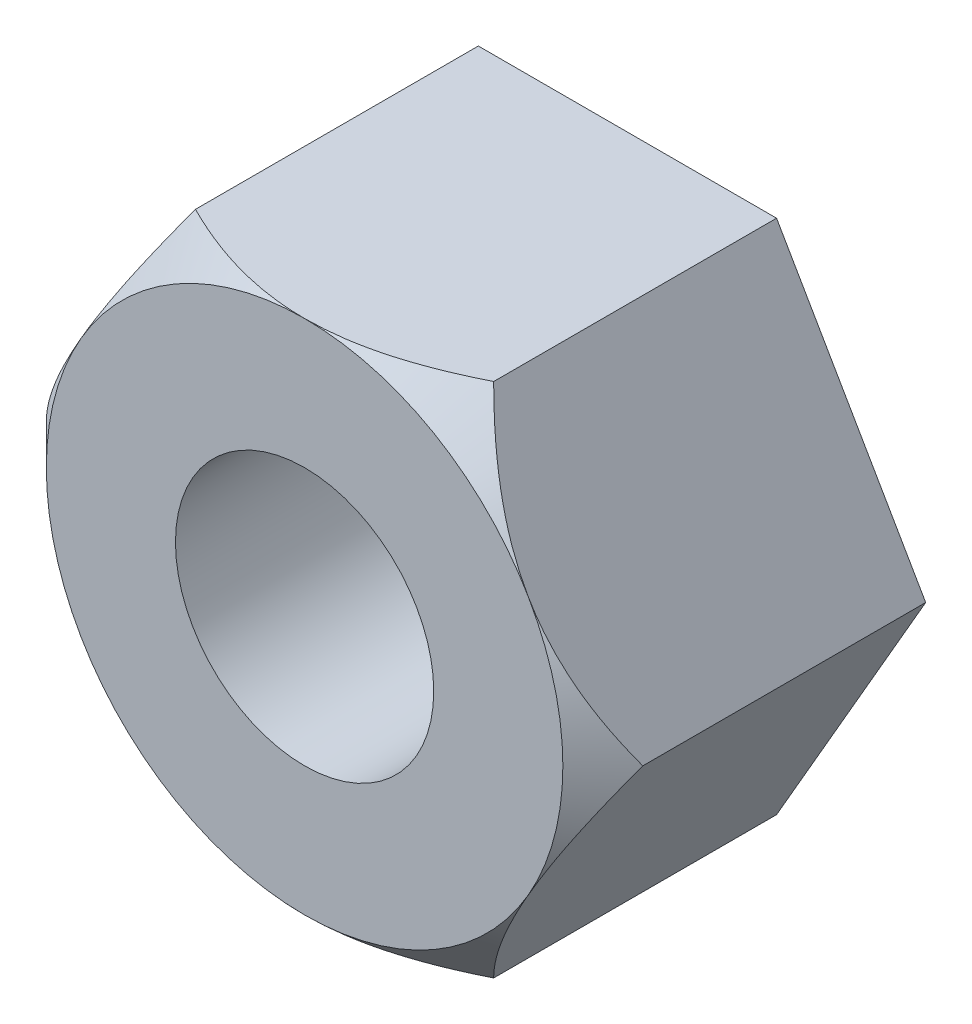
SolidWorks part; units mm, degrees
material "AISI 1020"
ref_plane "Plano frontal" through (0, 0, 0) normal (0, 0, 1) x (1, 0, 0)
ref_plane "Plano superior" through (0, 0, 0) normal (0, 1, 0) x (1, 0, 0)
ref_plane "Plano direito" through (0, 0, 0) normal (1, 0, 0) x (0, 0, -1)
sketch "Esboço1" plane through (0, 0, 0) normal (0, 0, 1) x (1, 0, 0)
  line L1 (2.3094, -4) -> (4.6188, 0)
  line L2 (4.6188, 0) -> (2.3094, 4)
  line L3 (2.3094, 4) -> (-2.3094, 4)
  line L4 (-2.3094, 4) -> (-4.6188, 0)
  line L5 (-4.6188, 0) -> (-2.3094, -4)
  line L6 (-2.3094, -4) -> (2.3094, -4)
  circle A0 centre (0, 0) radius 4 construction
  circle A1 centre (0, 0) radius 2
  dimension "D2" = 4
  dimension "D1" = 8
extrude "Ressalto-extrusão1" add sketch "Esboço1" along normal blind 5
sketch "Esboço2" plane through (0, 0, 5) normal (0, 0, 1) x (1, 0, 0)
  line L0 (2.3094, 4) -> (-2.3094, 4) construction
  circle A0 centre (0, 0) radius 4
  circle A1 centre (0, 0) radius 7.7502
extrude "Corte-extrusão1" cut sketch "Esboço2" against normal blind 1 draft 45
